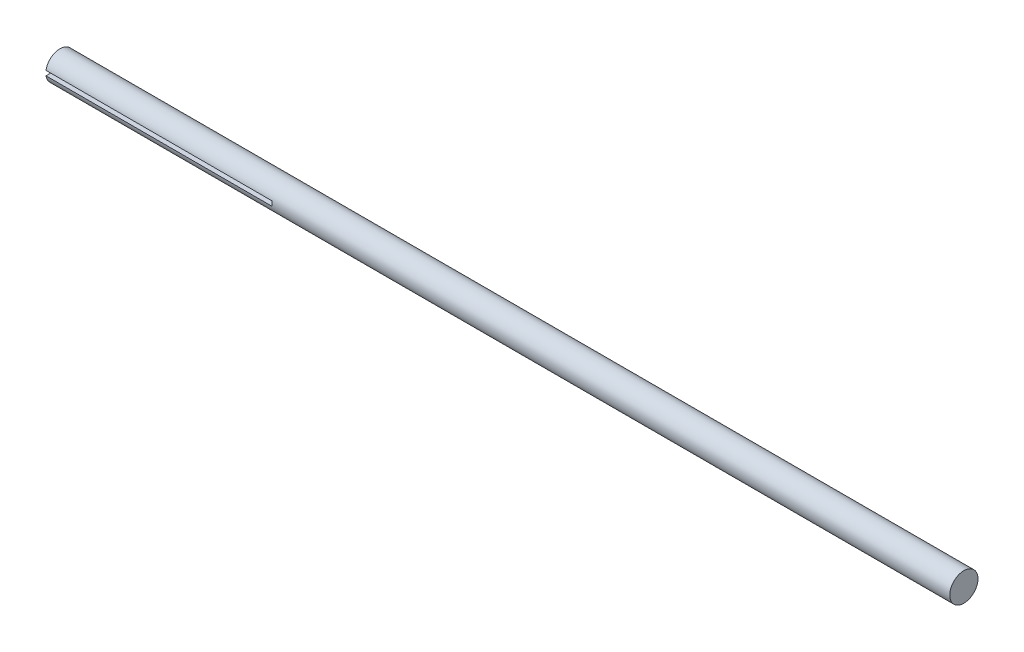
SolidWorks part; units mm, degrees
material "Mahogany"
ref_plane "Front Plane" through (0, 0, 0) normal (0, 0, 1) x (1, 0, 0)
ref_plane "Top Plane" through (0, 0, 0) normal (0, 1, 0) x (1, 0, 0)
ref_plane "Right Plane" through (0, 0, 0) normal (1, 0, 0) x (0, 0, -1)
sketch "Sketch1" plane through (0, 0, 0) normal (1, 0, 0) x (0, 0, -1)
  circle A0 centre (0, 0) radius 4.7625
  dimension "D1" = 9.525
extrude "Boss-Extrude1" add sketch "Sketch1" along normal blind 304.8
sketch "Sketch2" plane through (0, 0, 0) normal (-1, 0, 0) x (0, 0, 1)
  line L1 (6.35, 0.7938) -> (-6.35, 0.7937)
  line L2 (6.35, 0.7938) -> (6.35, -0.7937)
  line L3 (6.35, -0.7937) -> (-6.35, -0.7938)
  line L4 (-6.35, 0.7937) -> (-6.35, -0.7938)
  line L5 (6.35, 0.7938) -> (-6.35, -0.7938) construction
  line L6 (6.35, -0.7937) -> (-6.35, 0.7937) construction
  point P0 (0, 0)
  dimension "D1" = 1.5875
  dimension "D2" = 12.7
extrude "Cut-Extrude1" cut sketch "Sketch2" against normal blind 76.2
equation "\"D1@Sketch1\"=3in/8"
equation "\"D1@Boss-Extrude1\"=1ft"
equation "\"D1@Sketch2\"=1in/16"
equation "\"D2@Sketch2\"=.5in"
